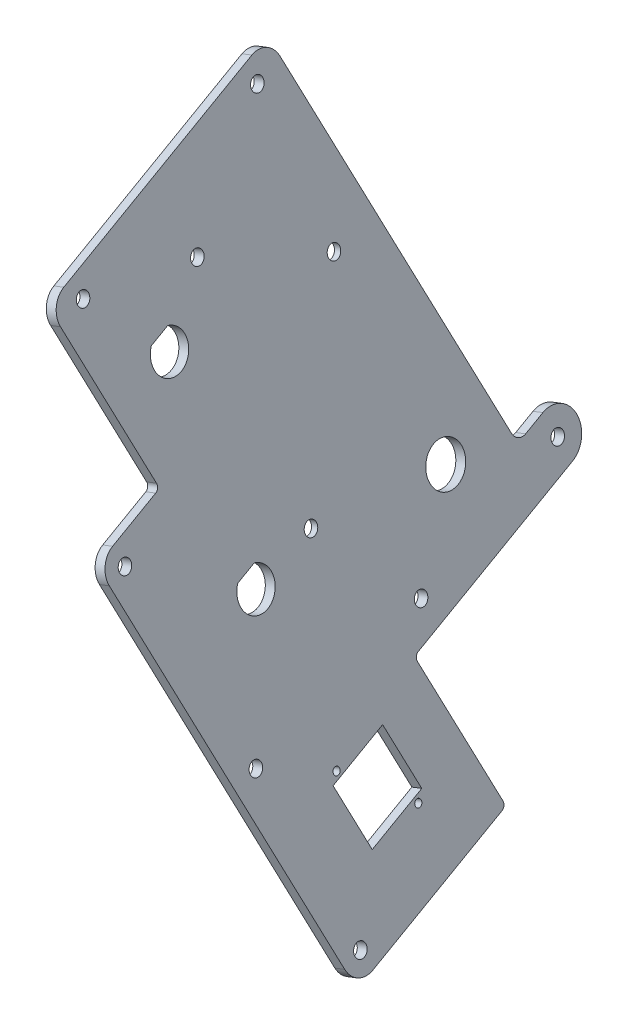
SolidWorks part; units mm, degrees
ref_plane "Front Plane" through (0, 0, 0) normal (0, 0, 1) x (1, 0, 0)
ref_plane "Top Plane" through (0, 0, 0) normal (0, 1, 0) x (1, 0, 0)
ref_plane "Right Plane" through (0, 0, 0) normal (1, 0, 0) x (0, 0, -1)
sketch "Sketch2" plane through (-64.0883, -22.3456, 3.4707) normal (0.943, 0.3288, -0.0511) x (-0.1539, 0.295, -0.943)
  line L9 (-121.8468, -165.7282) -> (-69.4593, -165.7282)
  line L10 (-67.8718, -164.1407) -> (-67.8718, -120.3257)
  line L11 (-66.2843, -118.7382) -> (-3.7368, -118.7382)
  line L12 (-3.7368, -103.4982) -> (-10.7218, -103.4982)
  line L13 (-13.8968, -100.3232) -> (-13.8968, 18.4218)
  line L14 (-20.2468, 24.7718) -> (-96.4468, 24.7718)
  line L15 (-102.7968, 18.4218) -> (-102.7968, -30.7907)
  line L16 (-104.3843, -32.3782) -> (-121.8468, -32.3782)
  line L17 (-128.1968, -38.7282) -> (-128.1968, -159.3782)
  line L18 (-121.8468, -165.7282) -> (-69.4593, -165.7282)
  line L19 (-67.8718, -164.1407) -> (-67.8718, -120.3257)
  line L20 (-66.2843, -118.7382) -> (-3.7368, -118.7382)
  line L21 (-3.7368, -103.4982) -> (-10.7218, -103.4982)
  line L22 (-13.8968, -100.3232) -> (-13.8968, 18.4218)
  line L23 (-20.2468, 24.7718) -> (-96.4468, 24.7718)
  line L24 (-102.7968, 18.4218) -> (-102.7968, -30.7907)
  line L25 (-104.3843, -32.3782) -> (-121.8468, -32.3782)
  line L26 (-128.1968, -38.7282) -> (-128.1968, -159.3782)
  arc A9 (-128.1968, -159.3782) -> (-121.8468, -165.7282) centre (-121.8468, -159.3782) ccw
  arc A10 (-69.4593, -165.7282) -> (-67.8718, -164.1407) centre (-69.4593, -164.1407) ccw
  arc A11 (-66.2843, -118.7382) -> (-67.8718, -120.3257) centre (-66.2843, -120.3257) ccw
  arc A12 (-3.7368, -118.7382) -> (-3.7368, -103.4982) centre (-3.7368, -111.1182) ccw
  arc A13 (-13.8968, -100.3232) -> (-10.7218, -103.4982) centre (-10.7218, -100.3232) ccw
  arc A14 (-13.8968, 18.4218) -> (-20.2468, 24.7718) centre (-20.2468, 18.4218) ccw
  arc A15 (-96.4468, 24.7718) -> (-102.7968, 18.4218) centre (-96.4468, 18.4218) ccw
  arc A16 (-104.3843, -32.3782) -> (-102.7968, -30.7907) centre (-104.3843, -30.7907) ccw
  arc A17 (-121.8468, -32.3782) -> (-128.1968, -38.7282) centre (-121.8468, -38.7282) ccw
  arc A18 (-128.1968, -159.3782) -> (-121.8468, -165.7282) centre (-121.8468, -159.3782) ccw
  arc A19 (-69.4593, -165.7282) -> (-67.8718, -164.1407) centre (-69.4593, -164.1407) ccw
  arc A20 (-66.2843, -118.7382) -> (-67.8718, -120.3257) centre (-66.2843, -120.3257) ccw
  arc A21 (-3.7368, -118.7382) -> (-3.7368, -103.4982) centre (-3.7368, -111.1182) ccw
  arc A22 (-13.8968, -100.3232) -> (-10.7218, -103.4982) centre (-10.7218, -100.3232) ccw
  arc A23 (-13.8968, 18.4218) -> (-20.2468, 24.7718) centre (-20.2468, 18.4218) ccw
  arc A24 (-96.4468, 24.7718) -> (-102.7968, 18.4218) centre (-96.4468, 18.4218) ccw
  arc A25 (-104.3843, -32.3782) -> (-102.7968, -30.7907) centre (-104.3843, -30.7907) ccw
  arc A26 (-121.8468, -32.3782) -> (-128.1968, -38.7282) centre (-121.8468, -38.7282) ccw
  dimension "D1" = 0
extrude "Boss-Extrude1" add sketch "Sketch2" against normal blind 3.175
hole_wizard "#6 Clearance Hole2" positions "Sketch7" profile "Sketch6" hole size "#6" standard "ANSI Inch" end condition through all
sketch "Sketch7" plane through (-67.0824, -23.3896, 3.6329) normal (-0.943, -0.3288, 0.0511) x (0.0482, 0.0168, 0.9987)
  point P0 (94.4966, -13.4386)
  point P3 (27.8213, 9.8091)
  point P6 (102.3032, -76.6848)
  point P9 (58.1833, -19.607)
  point P12 (18.6886, -122.85)
  point P15 (-33.0551, -106.1535)
  point P18 (79.3754, -137.621)
  point P21 (62.5815, -190.6085)
sketch "Sketch6" plane through (-58.1012, -34.4901, 98.0062) normal (-0.2039, 0.6923, 0.6923) x (0.263, -0.6424, 0.7198)
  line L0 (0, 0) -> (0, 74.7083)
  line L1 (0, 74.7083) -> (2.1526, 74.7083)
  line L2 (2.1526, 74.7083) -> (2.1526, 0)
  line L5 (2.1526, 0) -> (0, 0)
  line L11 (0, -6.35) -> (0, 107.95) construction
  dimension "Thru Hole Dia." = 4.3053
  dimension "Thru Hole Depth" = 74.7083
sketch "Sketch11" plane through (-30.1993, -118.7695, 70.6064) normal (-0.943, -0.3288, 0.0511) x (0.1539, -0.295, 0.943)
  line L0 (-5.4434, 7.7862) -> (1.2188, 7.7862)
  arc A0 (-5.4434, 7.7862) -> (1.2188, 7.7862) centre (-2.1123, 2.6808) ccw
  point P4 (-2.1123, -3.4152)
  dimension "D1" = 12.192
  dimension "D2" = 11.2014
extrude "Cut-Extrude1" cut sketch "Sketch11" against normal through all
other "Smart-Feature1<SxAL-1>"
sketch "Sketch111" plane through (-50.4713, -59.4826, 77.9843) normal (-0.943, -0.3288, 0.0511) x (0.1539, -0.295, 0.943)
  line L0 (-5.4434, 7.7862) -> (1.2188, 7.7862)
  arc A0 (-5.4434, 7.7862) -> (1.2188, 7.7862) centre (-2.1123, 2.6808) ccw
  point P4 (-2.1123, -3.4152)
  dimension "D1" = 12.192
  dimension "D2" = 11.2014
extrude "Cut-Extrude11" cut sketch "Sketch111" against normal through all
other "Smart-Feature2<SxAL-2>"
sketch "Sketch112" plane through (-67.0824, -23.3896, 3.6329) normal (-0.943, -0.3288, 0.0511) x (0.0482, 0.0168, 0.9987)
  line L0 (51.3191, -169.8693) -> (33.3311, -163.5975) construction
  line L1 (33.3311, -163.5975) -> (39.603, -145.6095) construction
  line L2 (39.603, -145.6095) -> (57.5909, -151.8814) construction
  line L3 (57.5909, -151.8814) -> (51.3191, -169.8693) construction
  line L4 (51.6315, -170.5162) -> (32.6842, -163.9099)
  line L5 (32.6842, -163.9099) -> (39.2906, -144.9626)
  line L6 (39.2906, -144.9626) -> (58.2379, -151.5689)
  line L7 (58.2379, -151.5689) -> (51.6315, -170.5162)
  circle A0 centre (1.5288, -97.2301) radius 6.35
  dimension "D1" = 12.7
  dimension "D2" = 0.508
extrude "Cut-Extrude13" cut sketch "Sketch112" against normal through all
hole_wizard "CSK for #6 Flat Head Machine Screw (100)1" positions "Sketch113" profile "Sketch114" countersink size "#6" standard "ANSI Inch" end condition through all
sketch "Sketch113" plane through (-67.0824, -23.3896, 3.6329) normal (-0.943, -0.3288, 0.0511) x (0.0482, 0.0168, 0.9987)
  point P5 (18.1068, -36.5682)
  point P7 (45.4444, -93.1744)
sketch "Sketch114" plane through (-54.1699, -57.6146, 21.7161) normal (-0.2039, 0.6923, 0.6923) x (0.263, -0.6424, 0.7198)
  line L0 (0, 0) -> (0, 74.7083)
  line L1 (0, 74.7083) -> (2.1526, 74.7083)
  line L2 (2.1526, 74.7083) -> (2.1526, 1.1669)
  line L3 (2.1526, 1.1669) -> (3.5433, 0)
  line L5 (3.5433, 0) -> (0, 0)
  line L6 (-2.1526, 1.1669) -> (-3.5433, 0) construction
  line L11 (0, -6.35) -> (0, 107.95) construction
  dimension "Thru Hole Dia." = 4.3053
  dimension "Thru Hole Depth" = 74.7083
  dimension "Near C'Sink Dia." = 7.0866
  dimension "Near C'Sink Angle" = 100
hole_wizard "#2 Clearance Hole1" positions "Sketch115" profile "Sketch116" hole size "#2" standard "ANSI Inch" end condition up to next
sketch "Sketch115" plane through (-64.0883, -22.3456, 3.4707) normal (0.943, 0.3288, -0.0511) x (-0.0482, -0.0168, -0.9987)
  point P0 (-34.7957, -166.6299)
  point P2 (-56.1264, -148.8489)
sketch "Sketch116" plane through (-7.5507, -179.1008, 38.221) normal (-0.2039, 0.6923, 0.6923) x (-0.263, 0.6424, -0.7198)
  line L0 (0, 0) -> (0, 3.175)
  line L1 (0, 3.175) -> (1.1303, 3.175)
  line L2 (1.1303, 3.175) -> (1.1303, 0)
  line L5 (1.1303, 0) -> (0, 0)
  line L11 (0, -6.35) -> (0, 107.95) construction
  dimension "Thru Hole Dia." = 2.2606
  dimension "Thru Hole Depth" = 3.175
